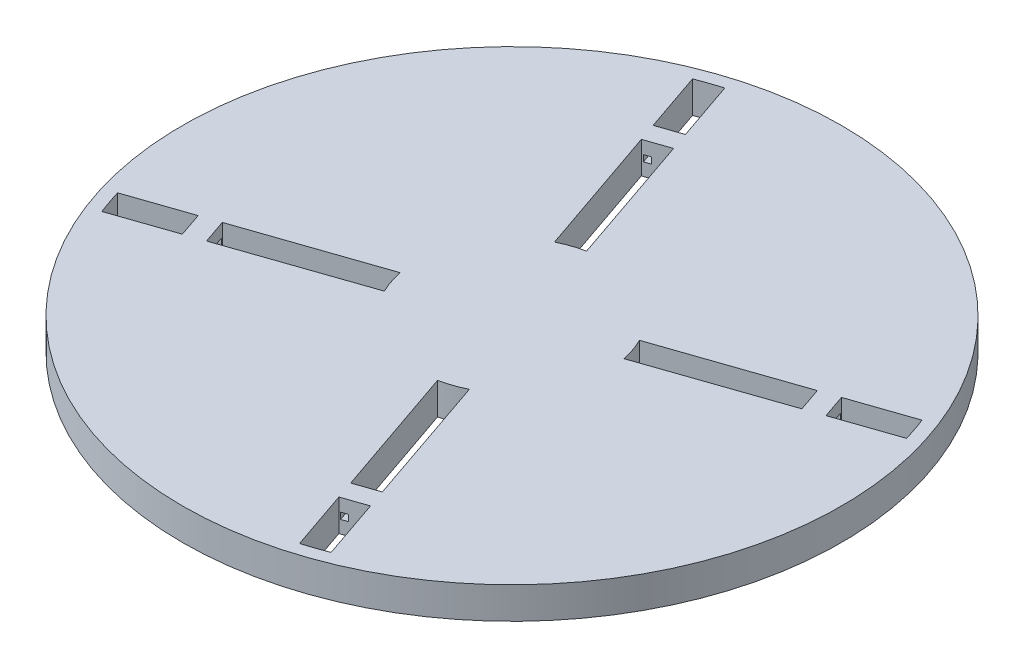
SolidWorks part; units mm, degrees
ref_plane "Front Plane" through (0, 0, 0) normal (0, 0, 1) x (1, 0, 0)
ref_plane "Top Plane" through (0, 0, 0) normal (0, 1, 0) x (1, 0, 0)
ref_plane "Right Plane" through (0, 0, 0) normal (1, 0, 0) x (0, 0, -1)
sketch "Sketch1" plane through (0, 0, 0) normal (0, 1, 0) x (1, 0, 0)
  circle A0 centre (0, 0) radius 52
extrude "Boss-Extrude1" add sketch "Sketch1" along normal blind 5
sketch "Sketch4" plane through (0, 0, 0) normal (0, -1, 0) x (1, 0, 0)
  line L0 (-30.2752, 23.3284) -> (-34.0461, 26.6125)
  line L1 (-26.7556, 22.7817) -> (-26.0018, 22.1287)
  line L2 (-26.0018, 22.1287) -> (-24.3606, 24.023)
  line L3 (-37.9034, -4.9121) -> (-42.8921, -5.2563)
  line L4 (-35.0281, -2.81) -> (-34.0334, -2.7387)
  line L5 (-34.0334, -2.7387) -> (-34.2124, -0.2387)
  line L6 (-34.2124, -0.2387) -> (-42.2124, -0.8116)
  line L7 (-42.2124, -0.8116) -> (-42.0556, -3.0012)
  line L8 (-24.3606, 24.023) -> (-30.4226, 29.2748)
  line L9 (-30.4226, 29.2748) -> (-31.86, 27.6156)
  line L10 (-37.9034, -4.9121) -> (-34.8925, -4.7043)
  line L11 (-42.8921, -5.2563) -> (-43.0427, -3.0741)
  line L12 (-30.2752, 23.3284) -> (-27.9992, 21.3462)
  line L13 (-43.0427, -3.0741) -> (-42.0556, -3.0012)
  line L14 (-34.8925, -4.7043) -> (-35.0281, -2.81)
  line L15 (-34.0461, 26.6125) -> (-32.6095, 28.262)
  line L16 (-32.6095, 28.262) -> (-31.86, 27.6156)
  line L17 (-27.9992, 21.3462) -> (-26.7556, 22.7817)
  line L18 (-4.9121, 37.9034) -> (-5.2563, 42.8921)
  line L19 (-2.81, 35.0281) -> (-2.7387, 34.0334)
  line L20 (-2.7387, 34.0334) -> (-0.2387, 34.2124)
  line L21 (-0.2387, 34.2124) -> (-0.8116, 42.2124)
  line L22 (-0.8116, 42.2124) -> (-3.0012, 42.0556)
  line L23 (-4.9121, 37.9034) -> (-4.7043, 34.8925)
  line L24 (-5.2563, 42.8921) -> (-3.0741, 43.0427)
  line L25 (-3.0741, 43.0427) -> (-3.0012, 42.0556)
  line L26 (-4.7043, 34.8925) -> (-2.81, 35.0281)
  line L27 (23.3284, 30.2752) -> (26.6125, 34.0461)
  line L28 (22.7817, 26.7556) -> (22.1287, 26.0018)
  line L29 (22.1287, 26.0018) -> (24.023, 24.3606)
  line L30 (24.023, 24.3606) -> (29.2748, 30.4226)
  line L31 (29.2748, 30.4226) -> (27.6156, 31.86)
  line L32 (23.3284, 30.2752) -> (21.3462, 27.9992)
  line L33 (26.6125, 34.0461) -> (28.262, 32.6095)
  line L34 (28.262, 32.6095) -> (27.6156, 31.86)
  line L35 (21.3462, 27.9992) -> (22.7817, 26.7556)
  line L36 (37.9034, 4.9121) -> (42.8921, 5.2563)
  line L37 (35.0281, 2.81) -> (34.0334, 2.7387)
  line L38 (34.0334, 2.7387) -> (34.2124, 0.2387)
  line L39 (34.2124, 0.2387) -> (42.2124, 0.8116)
  line L40 (42.2124, 0.8116) -> (42.0556, 3.0012)
  line L41 (37.9034, 4.9121) -> (34.8925, 4.7043)
  line L42 (42.8921, 5.2563) -> (43.0427, 3.0741)
  line L43 (43.0427, 3.0741) -> (42.0556, 3.0012)
  line L44 (34.8925, 4.7043) -> (35.0281, 2.81)
  line L45 (30.2752, -23.3284) -> (34.0461, -26.6125)
  line L46 (26.7556, -22.7817) -> (26.0018, -22.1287)
  line L47 (26.0018, -22.1287) -> (24.3606, -24.023)
  line L48 (24.3606, -24.023) -> (30.4226, -29.2748)
  line L49 (30.4226, -29.2748) -> (31.86, -27.6156)
  line L50 (30.2752, -23.3284) -> (27.9992, -21.3462)
  line L51 (34.0461, -26.6125) -> (32.6095, -28.262)
  line L52 (32.6095, -28.262) -> (31.86, -27.6156)
  line L53 (27.9992, -21.3462) -> (26.7556, -22.7817)
  line L54 (4.9121, -37.9034) -> (5.2563, -42.8921)
  line L55 (2.81, -35.0281) -> (2.7387, -34.0334)
  line L56 (2.7387, -34.0334) -> (0.2387, -34.2124)
  line L57 (0.2387, -34.2124) -> (0.8116, -42.2124)
  line L58 (0.8116, -42.2124) -> (3.0012, -42.0556)
  line L59 (4.9121, -37.9034) -> (4.7043, -34.8925)
  line L60 (5.2563, -42.8921) -> (3.0741, -43.0427)
  line L61 (3.0741, -43.0427) -> (3.0012, -42.0556)
  line L62 (4.7043, -34.8925) -> (2.81, -35.0281)
  line L63 (-23.3284, -30.2752) -> (-26.6125, -34.0461)
  line L64 (-22.7817, -26.7556) -> (-22.1287, -26.0018)
  line L65 (-22.1287, -26.0018) -> (-24.023, -24.3606)
  line L66 (-24.023, -24.3606) -> (-29.2748, -30.4226)
  line L67 (-29.2748, -30.4226) -> (-27.6156, -31.86)
  line L68 (-23.3284, -30.2752) -> (-21.3462, -27.9992)
  line L69 (-26.6125, -34.0461) -> (-28.262, -32.6095)
  line L70 (-28.262, -32.6095) -> (-27.6156, -31.86)
  line L71 (-21.3462, -27.9992) -> (-22.7817, -26.7556)
  point P77 (0, 0)
  dimension "D1" = 90
  dimension "D2" = 8
  dimension "D3" = 180
  dimension "D4" = 2.5
  dimension "D5" = 90
  dimension "D6" = 8
  dimension "D9" = 180
  dimension "D11" = 90
extrude "Cut-Extrude3" cut sketch "Sketch4" against normal blind 2.4
sketch "Sketch8" plane through (0, 0, 0) normal (0, -1, 0) x (1, 0, 0)
  line L0 (-47.9053, 14.3207) -> (-38.4434, 11.0781)
  line L1 (-46.6005, 18.1217) -> (-37.1439, 14.87)
  line L3 (2.9589, 14.7053) -> (10.1414, 35.5931)
  line L4 (13.4221, -6.6968) -> (34.3154, -13.8572)
  line L5 (6.6968, 13.4221) -> (13.8572, 34.3154)
  line L6 (14.7053, -2.9589) -> (35.5931, -10.1414)
  line L7 (-13.8931, -34.3031) -> (-6.7106, -13.4152)
  line L8 (-14.3207, -47.9053) -> (-11.0781, -38.4434)
  line L9 (-18.1217, -46.6005) -> (-14.87, -37.1439)
  line L10 (-11.0781, -38.4434) -> (-14.87, -37.1439)
  line L11 (-35.6055, 10.1055) -> (-34.3031, 13.8931)
  line L12 (-10.1055, -35.6055) -> (-13.8931, -34.3031)
  line L13 (-10.1055, -35.6055) -> (-2.9438, -14.7083)
  line L14 (-38.4434, 11.0781) -> (-37.1439, 14.87)
  line L15 (10.1414, 35.5931) -> (13.8572, 34.3154)
  line L16 (11.117, 38.4301) -> (14.8311, 37.1572)
  line L17 (35.5931, -10.1414) -> (34.3154, -13.8572)
  line L18 (38.4301, -11.117) -> (37.1572, -14.8311)
  line L19 (-34.3031, 13.8931) -> (-13.4152, 6.7106)
  line L20 (-35.6055, 10.1055) -> (-14.7083, 2.9438)
  line L21 (14.8311, 37.1572) -> (18.0738, 46.6191)
  line L22 (11.117, 38.4301) -> (14.37, 47.8905)
  line L23 (38.4301, -11.117) -> (47.8905, -14.37)
  line L24 (37.1572, -14.8311) -> (46.6191, -18.0738)
  arc A1 (18.0738, 46.6191) -> (14.37, 47.8905) centre (0, 0) ccw
  arc A2 (46.6191, -18.0738) -> (47.8905, -14.37) centre (0, 0) ccw
  arc A3 (-18.1217, -46.6005) -> (-14.3207, -47.9053) centre (0, 0) ccw
  arc A4 (-46.6005, 18.1217) -> (-47.9053, 14.3207) centre (0, 0) ccw
  arc A5 (-6.7106, -13.4152) -> (-2.9438, -14.7083) centre (0, 0) ccw
  arc A6 (13.4221, -6.6968) -> (14.7053, -2.9589) centre (0, 0) ccw
  arc A7 (6.6968, 13.4221) -> (2.9589, 14.7053) centre (0, 0) ccw
  arc A8 (-13.4152, 6.7106) -> (-14.7083, 2.9438) centre (0, 0) ccw
  point P14 (0, 0)
  point P40 (0, 0)
  dimension "D1" = 2
  dimension "D2" = 4
extrude "Cut-Extrude6" cut sketch "Sketch8" against normal blind 5
sketch "Sketch9" plane through (34.9481, 0, -12.0173) normal (-0.9457, 0, 0.3252) x (0.3252, 0, 0.9457)
  line L3 (0.769, 2.5) -> (0.769, 2)
  line L4 (0.769, 2) -> (1.769, 2)
  line L5 (1.769, 2) -> (1.769, 3)
  line L6 (1.769, 3) -> (0.769, 3)
  line L7 (0.769, 3) -> (0.769, 2.5)
  line L8 (-0.731, 2.5) -> (-0.731, 2)
  line L9 (-0.731, 2) -> (-1.731, 2)
  line L10 (-1.731, 2) -> (-1.731, 3)
  line L11 (-1.731, 3) -> (-0.731, 3)
  line L12 (-0.731, 3) -> (-0.731, 2.5)
extrude "Cut-Extrude7" cut sketch "Sketch9" against normal blind 5
pattern_circular "CirPattern1" count 4 every 90 about axis through (0, 0, 0) along (0, 1, 0) of "Cut-Extrude7"
